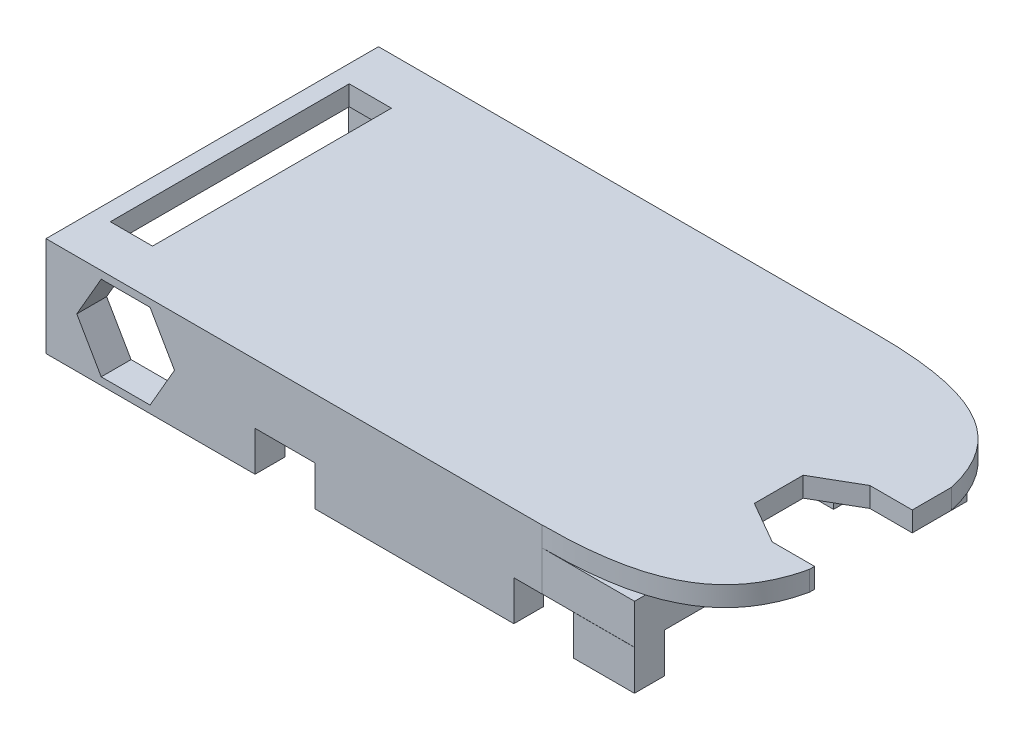
SolidWorks part; units mm, degrees
ref_plane "Front Plane" through (0, 0, 0) normal (0, 0, 1) x (1, 0, 0)
ref_plane "Top Plane" through (0, 0, 0) normal (0, 1, 0) x (1, 0, 0)
ref_plane "Right Plane" through (0, 0, 0) normal (1, 0, 0) x (0, 0, -1)
sketch "Sketch1" plane through (0, 0, 0) normal (0, 1, 0) x (1, 0, 0)
  line L1 (-40.0407, 20.9565) -> (-17.4855, 20.9565)
  line L2 (-40.0407, 20.9565) -> (-40.0407, 8.2565)
  line L3 (-40.0407, 8.2565) -> (-17.4855, 8.2565)
  line L4 (-17.4855, 20.9565) -> (-17.4855, 8.2565)
  dimension "D1" = 22.5552
  dimension "D2" = 12.7
extrude "Boss-Extrude1" add sketch "Sketch1" along normal blind 1
sketch "Sketch2" plane through (0, 1, 0) normal (0, 1, 0) x (1, 0, 0)
  line L0 (-17.4855, 20.9565) -> (-40.0407, 20.9565) construction
  line L1 (-40.0407, 18.2565) -> (-35.0407, 18.2565)
  line L2 (-40.0407, 18.2565) -> (-40.0407, 10.9565)
  line L3 (-40.0407, 10.9565) -> (-35.0407, 10.9565)
  line L4 (-35.0407, 18.2565) -> (-35.0407, 10.9565)
  line L7 (-40.0407, 20.9565) -> (-40.0407, 8.2565) construction
  dimension "D1" = 7.3
  dimension "D2" = 5
  dimension "D3" = 2.7
  dimension "D4" = 0
extrude "Cut-Extrude1" cut sketch "Sketch2" against normal blind 1
sketch "Sketch3" plane through (0, 1, 0) normal (0, 1, 0) x (1, 0, 0)
  line L0 (-17.4855, 8.2565) -> (-17.4855, 20.9565) construction
  line L1 (-17.4855, 16.2565) -> (-22.4855, 16.2565)
  line L2 (-17.4855, 16.2565) -> (-17.4855, 11.2565)
  line L3 (-17.4855, 11.2565) -> (-22.4855, 11.2565)
  line L4 (-22.4855, 16.2565) -> (-22.4855, 11.2565)
  line L5 (-40.0407, 8.2565) -> (-17.4855, 8.2565) construction
  line L6 (-17.4855, 20.9565) -> (-40.0407, 20.9565) construction
  dimension "D1" = 5
  dimension "D2" = 3
  dimension "D3" = 4.7
  dimension "D4" = 5
extrude "Cut-Extrude2" cut sketch "Sketch3" against normal blind 1
sketch "Sketch4" plane through (0, 0, 0) normal (0, -1, 0) x (1, 0, 0)
  line L0 (-17.4855, -8.2565) -> (-17.4855, -11.2565) construction
  line L1 (-40.0407, -8.2565) -> (-17.4855, -8.2565)
  line L2 (-40.0407, -8.2565) -> (-40.0407, -8.7565)
  line L3 (-40.0407, -8.7565) -> (-17.4855, -8.7565)
  line L4 (-17.4855, -8.2565) -> (-17.4855, -8.7565)
  line L5 (-40.0407, -20.9565) -> (-40.0407, -18.2565) construction
  line L6 (-17.4855, -8.2565) -> (-17.9855, -8.2565)
  line L7 (-17.4855, -8.2565) -> (-17.4855, -10.2565)
  line L8 (-17.4855, -10.2565) -> (-17.9855, -10.2565)
  line L9 (-17.9855, -8.2565) -> (-17.9855, -10.2565)
  line L10 (-40.0407, -20.4565) -> (-17.4855, -20.4565)
  line L11 (-40.0407, -20.4565) -> (-40.0407, -20.9565)
  line L12 (-40.0407, -20.9565) -> (-17.4855, -20.9565)
  line L13 (-17.4855, -20.4565) -> (-17.4855, -20.9565)
  line L15 (-17.4855, -20.9565) -> (-17.9855, -20.9565)
  line L16 (-17.4855, -20.9565) -> (-17.4855, -18.4565)
  line L17 (-17.4855, -18.4565) -> (-17.9855, -18.4565)
  line L18 (-17.9855, -20.9565) -> (-17.9855, -18.4565)
  line M3 (-17.4855, -11.2565) -> (-17.4855, -8.2565)
  line M5 (-40.0407, -8.2565) -> (-40.0407, -10.9565)
  line M9 (-40.0407, -18.2565) -> (-40.0407, -20.9565)
  line M10 (-40.0407, -20.9565) -> (-17.4855, -20.9565)
  line M11 (-17.4855, -20.9565) -> (-17.4855, -16.2565)
  dimension "D1" = 0.5
  dimension "D2" = 0.5
  dimension "D3" = 2
  dimension "D4" = 0.5
  dimension "D5" = 2.5
extrude "Boss-Extrude2" add sketch "Sketch4" along normal blind 1 contours L9 L1 L3 M5 | L3 L9 L8 M3 | L18 L10 L17 M11 | L18 L12 L10 M11 | L18 L10 M10 M9
sketch "Sketch5" plane through (0, 1, 0) normal (0, 1, 0) x (1, 0, 0)
  line L0 (-40.0407, 20.9565) -> (-40.0407, 18.2565) construction
  line L1 (-47.0407, 22.9565) -> (-13.4855, 22.9565)
  line L2 (-47.0407, 22.9565) -> (-47.0407, 6.2565)
  line L3 (-47.0407, 6.2565) -> (-13.4855, 6.2565)
  line L4 (-13.4855, 22.9565) -> (-13.4855, 6.2565)
  line L5 (-17.4855, 20.9565) -> (-40.0407, 20.9565) construction
  line L6 (-40.0407, 8.2565) -> (-17.4855, 8.2565) construction
  line L7 (-17.4855, 16.2565) -> (-17.4855, 20.9565) construction
  dimension "D1" = 7
  dimension "D2" = 2
  dimension "D3" = 2
  dimension "D4" = 4
extrude "Boss-Extrude3" add sketch "Sketch5" along normal blind 1
sketch "Sketch7" plane through (0, 1, 0) normal (0, -1, 0) x (-1, 0, 0)
  line L0 (13.4855, 6.2565) -> (13.4855, 22.9565) construction
  line L1 (17.7355, 14.9834) -> (15.6105, 16.2103)
  line L2 (15.6105, 16.2103) -> (13.4855, 14.9834)
  line L3 (13.4855, 14.9834) -> (13.4855, 12.5297)
  line L4 (13.4855, 12.5297) -> (15.6105, 11.3028)
  line L5 (15.6105, 11.3028) -> (17.7355, 12.5297)
  line L6 (17.7355, 12.5297) -> (17.7355, 14.9834)
  circle A0 centre (15.6105, 13.7565) radius 2.125 construction
  dimension "D1" = 4.25
  dimension "D2" = 0
extrude "Cut-Extrude4" cut sketch "Sketch7" against normal blind 1
sketch "Sketch8" plane through (0, 2, 0) normal (0, 1, 0) x (1, 0, 0)
  line L0 (-13.4855, 22.9565) -> (-47.0407, 22.9565) construction
  line L1 (-13.4855, 14.9834) -> (-13.4855, 22.9565) construction
  spline S0 degree 3 poles (-22.1278, 22.9565) (-17.368, 22.9565) (-14.3027, 21.872) (-13.4855, 18.1762) knots 0 0 0 0 1 1 1 1
extrude "Cut-Extrude5" cut sketch "Sketch8" along direction (0, 1, 0) on the side against the normal through all and the other way through all
sketch "Sketch9" plane through (0, 2, 0) normal (0, 1, 0) x (1, 0, 0)
  line L0 (-22.1278, 22.9565) -> (-47.0407, 22.9565) construction
  line L1 (-47.0407, 6.2565) -> (-13.4855, 6.2565) construction
  point P0 (-32.2929, 14.6065)
  dimension "D1" = 8.35
  dimension "D2" = 8.35
ref_plane "Plane1" through (0, 0, -14.61) normal (0, 0, 1) x (1, 0, 0)
mirror "Mirror2" about plane through (0, 0, -14.61) normal (0, 0, 1) of "Cut-Extrude5"
sketch "Sketch10" plane through (0, 1, 0) normal (0, -1, 0) x (-1, 0, 0)
  line L0 (40.0407, 8.2565) -> (17.4855, 8.2565) construction
  line L1 (40.0407, 6.2565) -> (17.4855, 6.2565)
  line L2 (40.0407, 6.2565) -> (40.0407, 8.2565)
  line L3 (40.0407, 8.2565) -> (17.4855, 8.2565)
  line L4 (17.4855, 6.2565) -> (17.4855, 8.2565)
  line L5 (40.0407, 20.9565) -> (17.4855, 20.9565) construction
  line L6 (40.0407, 22.9565) -> (17.4855, 22.9565)
  line L7 (40.0407, 22.9565) -> (40.0407, 20.9565)
  line L8 (40.0407, 20.9565) -> (17.4855, 20.9565)
  line L9 (17.4855, 22.9565) -> (17.4855, 20.9565)
  line L10 (17.4855, 8.2565) -> (17.4855, 11.2565) construction
  line L11 (17.4855, 16.2565) -> (17.4855, 20.9565) construction
  dimension "D1" = 0
  dimension "D2" = 0
extrude "Boss-Extrude4" add sketch "Sketch10" along normal blind 2
sketch "Sketch11" plane through (0, 2, 0) normal (0, 1, 0) x (1, 0, 0)
  line L1 (-22.1278, 6.2635) -> (-13.2079, 6.2635)
  line L2 (-22.1278, 6.2635) -> (-22.1278, 5.533)
  line L3 (-22.1278, 5.533) -> (-13.2079, 5.533)
  line L4 (-13.2079, 6.2635) -> (-13.2079, 5.533)
extrude "Cut-Extrude6" cut sketch "Sketch11" against normal blind 3
sketch "Sketch12" plane through (0, -1, 0) normal (0, -1, 0) x (-1, 0, 0)
  line L0 (17.4855, 10.2565) -> (17.4855, 6.2635) construction
  line L1 (40.0407, 6.2565) -> (17.4855, 6.2565)
  line L2 (40.0407, 6.2565) -> (40.0407, 7.7565)
  line L3 (40.0407, 7.7565) -> (17.4855, 7.7565)
  line L4 (17.4855, 6.2565) -> (17.4855, 7.7565)
  line L5 (17.4855, 22.4089) -> (17.4855, 16.2565) construction
  line L6 (40.0407, 22.9565) -> (17.4855, 22.9565)
  line L7 (40.0407, 22.9565) -> (40.0407, 21.4565)
  line L8 (40.0407, 21.4565) -> (17.4855, 21.4565)
  line L9 (17.4855, 22.9565) -> (17.4855, 21.4565)
  dimension "D1" = 1.5
  dimension "D2" = 1.5
extrude "Boss-Extrude5" add sketch "Sketch12" along normal blind 2
sketch "Sketch13" plane through (0, -3, 0) normal (0, -1, 0) x (-1, 0, 0)
  line L0 (17.4855, 6.2565) -> (40.0407, 6.2565) construction
  line L1 (36.5407, 6.2565) -> (33.5407, 6.2565)
  line L2 (36.5407, 6.2565) -> (36.5407, 7.7565)
  line L3 (36.5407, 7.7565) -> (33.5407, 7.7565)
  line L4 (33.5407, 6.2565) -> (33.5407, 7.7565)
  line L5 (40.0407, 7.7565) -> (17.4855, 7.7565) construction
  line L6 (17.4855, 21.4565) -> (40.0407, 21.4565) construction
  line L7 (36.5407, 21.4565) -> (33.5407, 21.4565)
  line L8 (36.5407, 21.4565) -> (36.5407, 22.9565)
  line L9 (36.5407, 22.9565) -> (33.5407, 22.9565)
  line L10 (33.5407, 21.4565) -> (33.5407, 22.9565)
  line L11 (40.0407, 22.9565) -> (17.4855, 22.9565) construction
  line L12 (40.0407, 6.2565) -> (40.0407, 7.7565) construction
  line L13 (23.5407, 6.2565) -> (23.5407, 7.7565)
  line L14 (23.5407, 6.2565) -> (20.5407, 6.2565)
  line L15 (20.5407, 6.2565) -> (20.5407, 7.7565)
  line L16 (23.5407, 7.7565) -> (20.5407, 7.7565)
  line L17 (23.5407, 21.4565) -> (23.5407, 22.9565)
  line L18 (23.5407, 21.4565) -> (20.5407, 21.4565)
  line L19 (20.5407, 21.4565) -> (20.5407, 22.9565)
  line L20 (23.5407, 22.9565) -> (20.5407, 22.9565)
  line L21 (17.4855, 7.7565) -> (17.4855, 6.2565) construction
  dimension "D1" = 3
  dimension "D2" = 3.5
  dimension "D3" = 0
  dimension "D4" = 3
  dimension "D6" = 3.0552
  dimension "D5" = 2
extrude "Cut-Extrude7" cut sketch "Sketch13" against normal blind 2
sketch "Sketch14" plane through (0, 2, 0) normal (0, 1, 0) x (1, 0, 0)
  line L1 (-15.6105, 16.2103) -> (-13.4855, 16.2103)
  line L2 (-15.6105, 16.2103) -> (-15.6105, 14.9834)
  line L3 (-15.6105, 14.9834) -> (-13.4855, 14.9834)
  line L4 (-13.4855, 16.2103) -> (-13.4855, 14.9834)
  line L5 (-15.6105, 11.3028) -> (-13.4855, 11.3028)
  line L6 (-15.6105, 11.3028) -> (-15.6105, 12.5297)
  line L7 (-15.6105, 12.5297) -> (-13.4855, 12.5297)
  line L8 (-13.4855, 11.3028) -> (-13.4855, 12.5297)
extrude "Cut-Extrude8" cut sketch "Sketch14" against normal blind 1
sketch "Sketch15" plane through (0, 1, 0) normal (0, -1, 0) x (-1, 0, 0)
  line L0 (47.0407, 6.2565) -> (40.0407, 6.2565) construction
  line L1 (44.0407, 20.6065) -> (46.1607, 20.6065)
  line L2 (44.0407, 20.6065) -> (44.0407, 8.6065)
  line L3 (44.0407, 8.6065) -> (46.1607, 8.6065)
  line L4 (46.1607, 20.6065) -> (46.1607, 8.6065)
  line L5 (40.0407, 22.9565) -> (47.0407, 22.9565) construction
  line L6 (40.0407, 10.9565) -> (40.0407, 6.2565) construction
  line L8 (47.0407, 22.9565) -> (47.0407, 6.2565) construction
  dimension "D1" = 12
  dimension "D2" = 2.12
  dimension "D3" = 2.35
  dimension "D4" = 2.35
  dimension "D5" = 4
  dimension "D6" = 0.88
extrude "adapter_PCB_hole" cut sketch "Sketch15" against normal blind 1
sketch "Sketch16" plane through (0, 1, 0) normal (0, -1, 0) x (-1, 0, 0)
  line L0 (47.0407, 22.9565) -> (47.0407, 6.2565) construction
  line L1 (40.0407, 22.9565) -> (47.0407, 22.9565)
  line L2 (40.0407, 22.9565) -> (40.0407, 21.4565)
  line L3 (40.0407, 21.4565) -> (47.0407, 21.4565)
  line L4 (47.0407, 22.9565) -> (47.0407, 21.4565)
  line L5 (36.5407, 21.4565) -> (40.0407, 21.4565) construction
  dimension "D1" = 0
extrude "Boss-Extrude6" add sketch "Sketch16" along normal blind 4
sketch "Sketch19" plane through (0, 0, -22.9565) normal (0, 0, -1) x (-1, 0, 0)
  line L0 (22.1278, 2) -> (47.0407, 2) construction
  line L1 (45.4944, -0.5) -> (44.2676, 1.625)
  line L2 (44.2676, 1.625) -> (41.8138, 1.625)
  line L3 (41.8138, 1.625) -> (40.587, -0.5)
  line L4 (40.587, -0.5) -> (41.8138, -2.625)
  line L5 (41.8138, -2.625) -> (44.2676, -2.625)
  line L6 (44.2676, -2.625) -> (45.4944, -0.5)
  line L7 (47.0407, -3) -> (36.5407, -3) construction
  line L8 (47.0407, 2) -> (47.0407, -3) construction
  circle A0 centre (43.0407, -0.5) radius 2.125 construction
  dimension "D1" = 2.5
  dimension "D2" = 2.5
  dimension "D3" = 4
extrude "nut_hole" cut sketch "Sketch19" against normal blind 1.5
sketch "Sketch20" plane through (0, 1, 0) normal (0, -1, 0) x (-1, 0, 0)
  line L0 (47.0407, 21.4565) -> (47.0407, 6.2565) construction
  line L1 (40.0407, 6.2565) -> (47.0407, 6.2565)
  line L2 (40.0407, 6.2565) -> (40.0407, 7.7565)
  line L3 (40.0407, 7.7565) -> (47.0407, 7.7565)
  line L4 (47.0407, 6.2565) -> (47.0407, 7.7565)
  line L5 (40.0407, 7.7565) -> (36.5407, 7.7565) construction
  dimension "D1" = 0
extrude "Boss-Extrude7" add sketch "Sketch20" along normal blind 4
sketch "Sketch21" plane through (0, 0, -6.2565) normal (0, 0, 1) x (1, 0, 0)
  line L0 (-47.0407, 2) -> (-22.1278, 2) construction
  line L1 (-45.4944, -0.5) -> (-44.2676, -2.625)
  line L2 (-44.2676, -2.625) -> (-41.8138, -2.625)
  line L3 (-41.8138, -2.625) -> (-40.587, -0.5)
  line L4 (-40.587, -0.5) -> (-41.8138, 1.625)
  line L5 (-41.8138, 1.625) -> (-44.2676, 1.625)
  line L6 (-44.2676, 1.625) -> (-45.4944, -0.5)
  line L7 (-47.0407, 2) -> (-47.0407, -3) construction
  circle A0 centre (-43.0407, -0.5) radius 2.125 construction
  dimension "D1" = 2.5
  dimension "D2" = 4
extrude "nut_hole2" cut sketch "Sketch21" against normal blind 1.5
